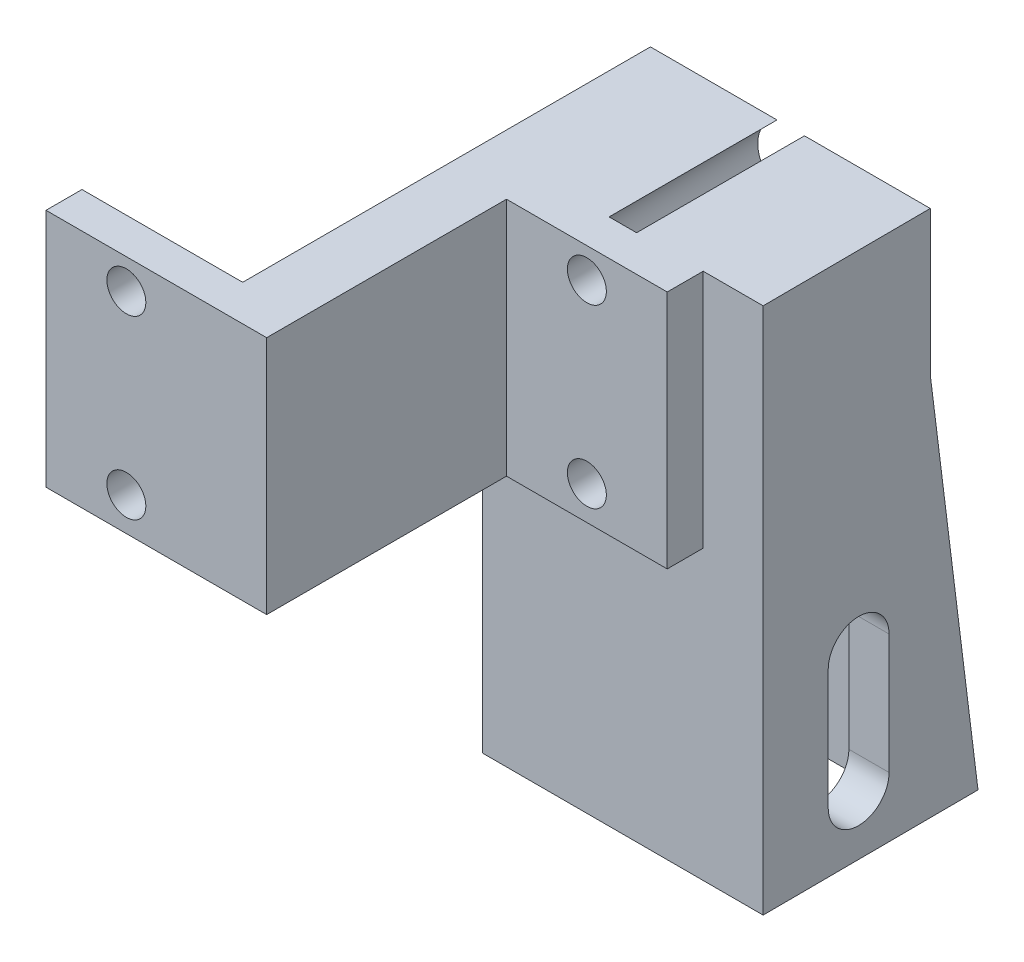
SolidWorks part; units mm, degrees
ref_plane "Front Plane" through (0, 0, 0) normal (0, 0, 1) x (1, 0, 0)
ref_plane "Top Plane" through (0, 0, 0) normal (0, 1, 0) x (1, 0, 0)
ref_plane "Right Plane" through (0, 0, 0) normal (1, 0, 0) x (0, 0, -1)
sketch "Sketch1" plane through (0, 0, 0) normal (0, 1, 0) x (1, 0, 0)
  line L0 (0, 0) -> (18.4, 0)
  line L1 (18.4, 0) -> (18.4, 20)
  line L2 (18.4, 20) -> (31.8, 20)
  line L3 (31.8, 20) -> (31.8, 23)
  line L4 (31.8, 23) -> (13.4, 23)
  line L5 (13.4, 23) -> (13.4, 3)
  line L6 (13.4, 3) -> (0, 3)
  line L7 (0, 3) -> (0, 0)
  dimension "D1" = 13.4
  dimension "D2" = 5
  dimension "D3" = 3
  dimension "D4" = 17
extrude "Boss-Extrude1" add sketch "Sketch1" along normal blind 20
sketch "Sketch2" plane through (0, 0, -20) normal (0, 0, 1) x (1, 0, 0)
  line L0 (25.1, 20) -> (25.1, 0) construction
  line L2 (18.4, 20) -> (31.8, 20) construction
  line L4 (18.4, 0) -> (31.8, 0) construction
  circle A0 centre (25.1, 17.5) radius 1.625
  circle A1 centre (25.1, 2.8) radius 1.625
  point P10 (25.1, 17.7566)
  point P11 (25.1, 6.3035)
  point P12 (25.1, 17.3285)
  dimension "D1" = 3.25
  dimension "D2" = 14.7
  dimension "D3" = 2.5
extrude "Cut-Extrude1" cut sketch "Sketch2" against normal through all both and the other way through all
ref_plane "Plane1" through (15.9, 0, 0) normal (-1, 0, 0) x (0, 0, 1)
mirror "Mirror1" about plane through (15.9, 0, 0) normal (-1, 0, 0) of "Cut-Extrude1"
sketch "Sketch3" plane through (13.4, 0, 0) normal (-1, 0, 0) x (0, 0, 1)
  line L0 (-23, 20) -> (-23, -24)
  line L1 (-23, -24) -> (-41, -24)
  line L2 (-41, -24) -> (-37, 8)
  line L3 (-37, 8) -> (-37, 20)
  line L4 (-37, 20) -> (-23, 20)
  line L5 (-23, 0) -> (-3, 0) construction
  line L6 (-31, -9) -> (-31, -19) construction
  line L7 (-28.45, -9) -> (-28.45, -19)
  line L8 (-33.55, -9) -> (-33.55, -19)
  arc A0 (-28.45, -9) -> (-33.55, -9) centre (-31, -9) ccw
  arc A1 (-33.55, -19) -> (-28.45, -19) centre (-31, -19) ccw
  point P10 (-31, -14)
  dimension "D1" = 12
  dimension "D2" = 14
  dimension "D3" = 24
  dimension "D4" = 18
  dimension "D5" = 10
  dimension "D6" = 5.1
  dimension "D7" = 8
  dimension "D8" = 5
extrude "Boss-Extrude2" add sketch "Sketch3" against normal offset from surface (23.4 mm away) 5 up to face at (31.8, 10, -21.5) offset beyond the face yes
sketch "Sketch4" plane through (0, -24, 0) normal (0, -1, 0) x (1, 0, 0)
  line L7 (36.8, -23) -> (36.7152, -41)
  line L8 (36.8, -41) -> (13.4, -41) construction
  line L9 (36.7152, -41) -> (36.8, -41)
  line L10 (36.8, -41) -> (36.8, -23)
  dimension "D1" = 0.27
sketch "Sketch5" plane through (0, 0, -23) normal (0, 0, 1) x (1, 0, 0)
  circle A0 centre (25.1, 17.5) radius 2.75
  circle A1 centre (25.1, 2.8) radius 2.75
  dimension "D1" = 5.5
extrude "Cut-Extrude2" cut sketch "Sketch5" against normal through all
extrude "Cut-Extrude3" cut sketch "Sketch4" against normal through all
sketch "Sketch7" plane through (13.4, 0, 0) normal (-1, 0, 0) x (0, 0, 1)
  line L0 (-37, -9) -> (-37, -24)
  line L1 (-41, -24) -> (-23, -24) construction
  line L2 (-37, -24) -> (-25, -24)
  line L3 (-25, -24) -> (-25, -9)
  arc A0 (-37, -9) -> (-25, -9) centre (-31, -9) cw
  arc A1 (-28.45, -9) -> (-33.55, -9) centre (-31, -9) ccw construction
  point P10 (0, 0)
  dimension "D1" = 6
extrude "Cut-Extrude4" cut sketch "Sketch7" against normal blind 20
